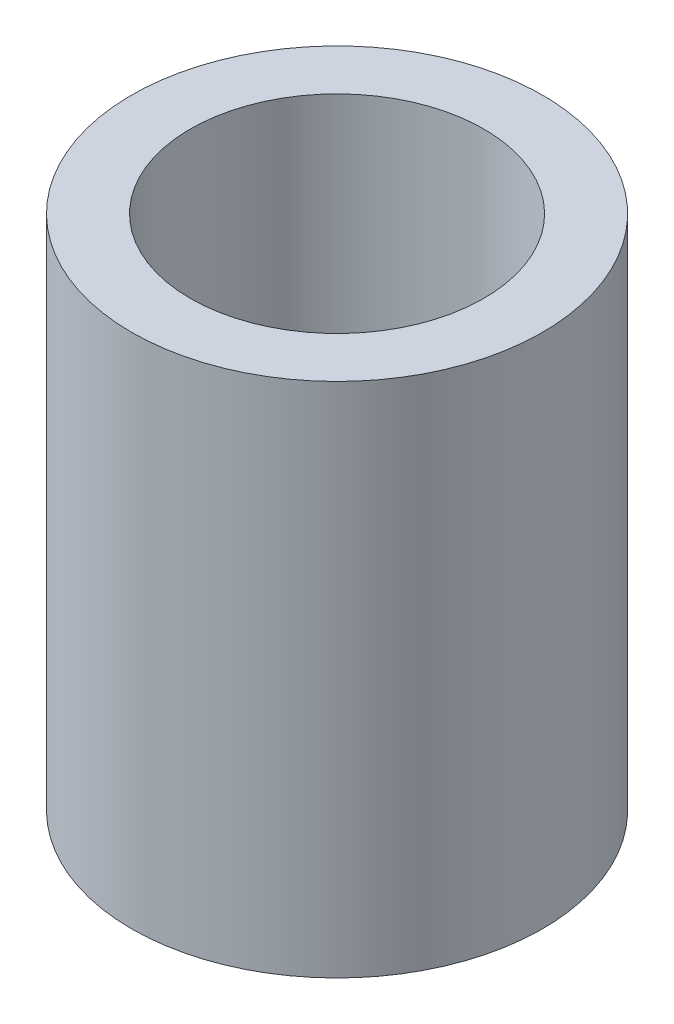
SolidWorks part; units mm, degrees
material "6061-T6 (SS)"
ref_plane "X-Y Datum" through (0, 0, 0) normal (0, 0, 1) x (1, 0, 0)
ref_plane "X-Z Datum" through (0, 0, 0) normal (0, 1, 0) x (1, 0, 0)
ref_plane "Y-Z Datum" through (0, 0, 0) normal (1, 0, 0) x (0, 0, -1)
sketch "Sketch1" plane through (0, 0, 0) normal (0, 1, 0) x (1, 0, 0)
  circle A0 centre (0, 0) radius 3.9688
  circle A1 centre (0, 0) radius 5.5562
  dimension "D1" = 7.9375
  dimension "D2" = 11.1125
  dimension "D3" = 1.5875
extrude "Boss-Extrude1" add sketch "Sketch1" against normal blind 13.97
